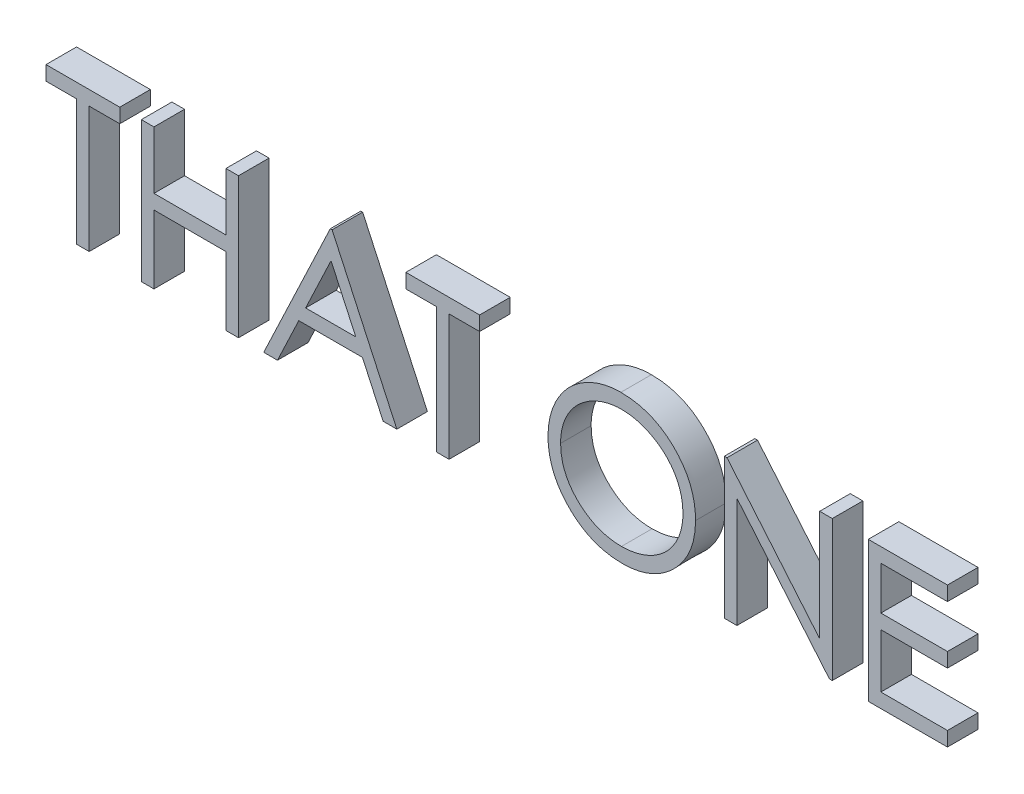
SolidWorks part; units mm, degrees
ref_plane "Front Plane" through (0, 0, 0) normal (0, 0, 1) x (1, 0, 0)
ref_plane "Top Plane" through (0, 0, 0) normal (0, 1, 0) x (1, 0, 0)
ref_plane "Right Plane" through (0, 0, 0) normal (1, 0, 0) x (0, 0, -1)
sketch "Sketch1" plane through (0, 0, 0) normal (0, 0, 1) x (1, 0, 0)
  text T0 "THAT ONE"
extrude "Boss-Extrude1" add sketch "Sketch1" along normal blind 0.762
